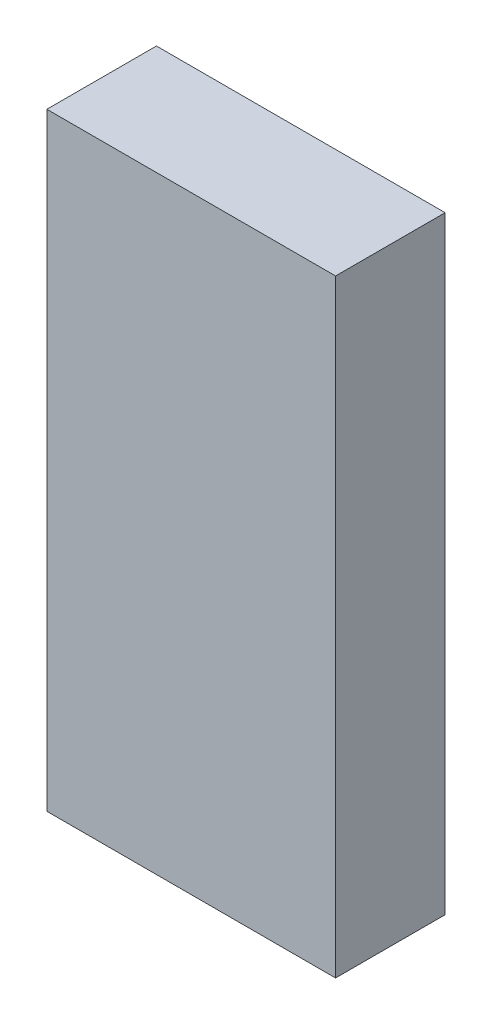
SolidWorks part; units mm, degrees
ref_plane "Front Plane" through (0, 0, 0) normal (0, 0, 1) x (1, 0, 0)
ref_plane "Top Plane" through (0, 0, 0) normal (0, 1, 0) x (1, 0, 0)
ref_plane "Right Plane" through (0, 0, 0) normal (1, 0, 0) x (0, 0, -1)
sketch "Sketch1" plane through (0, 0, 0) normal (0, 0, 1) x (1, 0, 0)
  line L1 (0, 0) -> (16.7323, 0)
  line L2 (0, 0) -> (0, -35.2363)
  line L3 (0, -35.2363) -> (16.7323, -35.2363)
  line L4 (16.7323, 0) -> (16.7323, -35.2363)
extrude "Boss-Extrude1" add sketch "Sketch1" along normal blind 6.35
